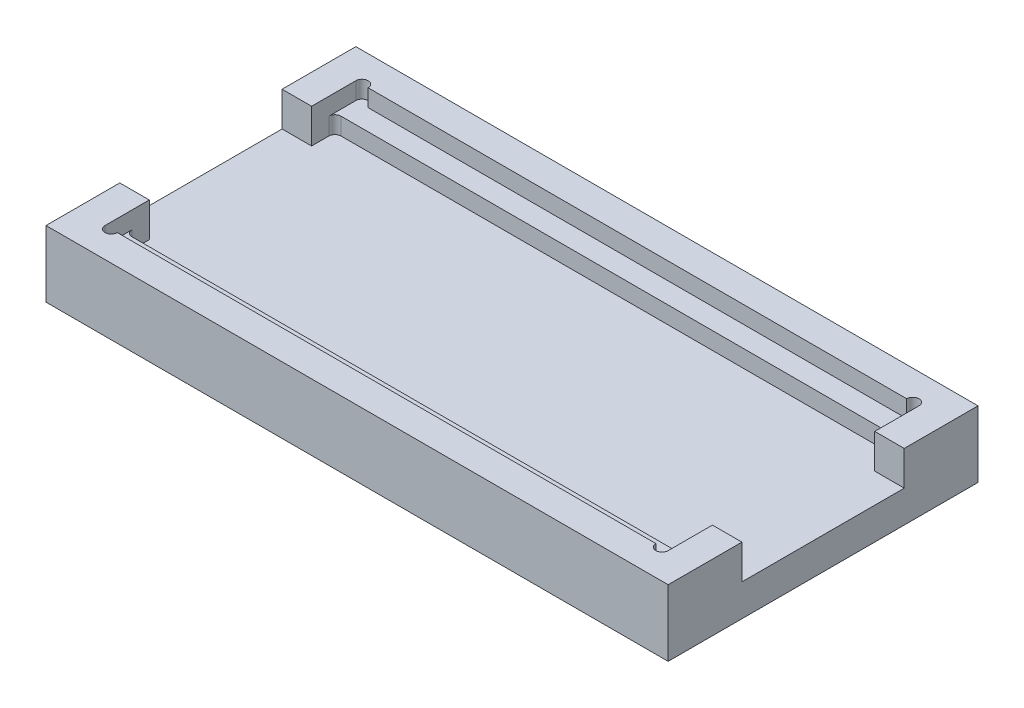
SolidWorks part; units mm, degrees
material "Delrin 2700 NC010, Low Viscosity Acetal Copolymer (SS)"
ref_plane "Front Plane" through (0, 0, 0) normal (0, 0, 1) x (1, 0, 0)
ref_plane "Top Plane" through (0, 0, 0) normal (0, 1, 0) x (1, 0, 0)
ref_plane "Right Plane" through (0, 0, 0) normal (1, 0, 0) x (0, 0, -1)
sketch "Sketch1" plane through (0, 0, 0) normal (0, 1, 0) x (1, 0, 0)
  line L1 (0, 0) -> (253, 0)
  line L2 (0, 0) -> (0, 126)
  line L3 (0, 126) -> (253, 126)
  line L4 (253, 0) -> (253, 126)
  dimension "D1" = 126
  dimension "D2" = 253
extrude "Boss-Extrude1" add sketch "Sketch1" along normal blind 27
sketch "Sketch2" plane through (0, 27, 0) normal (0, 1, 0) x (1, 0, 0)
  line L0 (0, 126) -> (0, 0) construction
  line L1 (12, 114) -> (241, 114)
  line L2 (12, 114) -> (12, 12)
  line L3 (12, 12) -> (241, 12)
  line L4 (241, 114) -> (241, 12)
  line L5 (0, 0) -> (253, 0) construction
  line L6 (253, 0) -> (253, 126) construction
  line L7 (253, 126) -> (0, 126) construction
  dimension "D1" = 12
  dimension "D2" = 12
  dimension "D3" = 12
  dimension "D4" = 12
extrude "Cut-Extrude1" cut sketch "Sketch2" against normal blind 7
sketch "Sketch3" plane through (0, 20, 0) normal (0, 1, 0) x (1, 0, 0)
  line L1 (241, 105.5) -> (12, 105.5)
  line L2 (241, 105.5) -> (241, 20.5)
  line L3 (241, 20.5) -> (12, 20.5)
  line L4 (12, 105.5) -> (12, 20.5)
  line L5 (241, 114) -> (12, 114) construction
  line L6 (12, 114) -> (12, 12) construction
  line L7 (241, 12) -> (241, 114) construction
  line L8 (12, 12) -> (241, 12) construction
  dimension "D1" = 8.5
  dimension "D3" = 8.5
extrude "Cut-Extrude2" cut sketch "Sketch3" against normal blind 7
sketch "Sketch4" plane through (0, 27, 0) normal (0, 1, 0) x (1, 0, 0)
  line L0 (0, 126) -> (0, 0) construction
  line L1 (0, 30) -> (12, 30)
  line L2 (0, 30) -> (0, 96)
  line L3 (0, 96) -> (12, 96)
  line L4 (12, 30) -> (12, 96)
  line L5 (12, 114) -> (12, 12) construction
  line L6 (0, 0) -> (253, 0) construction
  line L7 (253, 126) -> (0, 126) construction
  dimension "D1" = 30
  dimension "D2" = 30
extrude "Cut-Extrude3" cut sketch "Sketch4" against normal blind 14
sketch "Sketch5" plane through (0, 27, 0) normal (0, 1, 0) x (1, 0, 0)
  line L0 (253, 0) -> (253, 126) construction
  line L1 (253, 96) -> (241, 96)
  line L2 (253, 96) -> (253, 30)
  line L3 (253, 30) -> (241, 30)
  line L4 (241, 96) -> (241, 30)
  line L5 (241, 12) -> (241, 114) construction
  line L6 (0, 0) -> (253, 0) construction
  line L7 (253, 126) -> (0, 126) construction
  dimension "D1" = 30
  dimension "D2" = 30
extrude "Cut-Extrude4" cut sketch "Sketch5" against normal blind 14
sketch "Sketch6" plane through (0, 27, 0) normal (0, 1, 0) x (1, 0, 0)
  line L2 (12, 12) -> (241, 12) construction
  line L3 (12, 12) -> (17, 12)
  line L4 (12, 12) -> (241, 12) construction
  line L5 (236, 12) -> (241, 12)
  line L6 (241, 114) -> (12, 114) construction
  line L7 (12, 114) -> (17, 114)
  line L8 (236, 114) -> (241, 114)
  arc A1 (12, 12) -> (17, 12) centre (14.5, 12) ccw
  arc A2 (241, 12) -> (236, 12) centre (238.5, 12) cw
  arc A3 (12, 114) -> (17, 114) centre (14.5, 114) cw
  arc A4 (241, 114) -> (236, 114) centre (238.5, 114) ccw
  dimension "D1" = 2.5
  dimension "D2" = 2.5
  dimension "D3" = 2.5
  dimension "D4" = 2.5
extrude "Cut-Extrude5" cut sketch "Sketch6" against normal up to surface (7 mm away) up to face at (126.5, 20, -16.25)
fillet "Fillet1" radius 2.5 4 edges at (241, 16.5, -105.5) (241, 16.5, -20.5) (12, 16.5, -20.5) (12, 16.5, -105.5)
